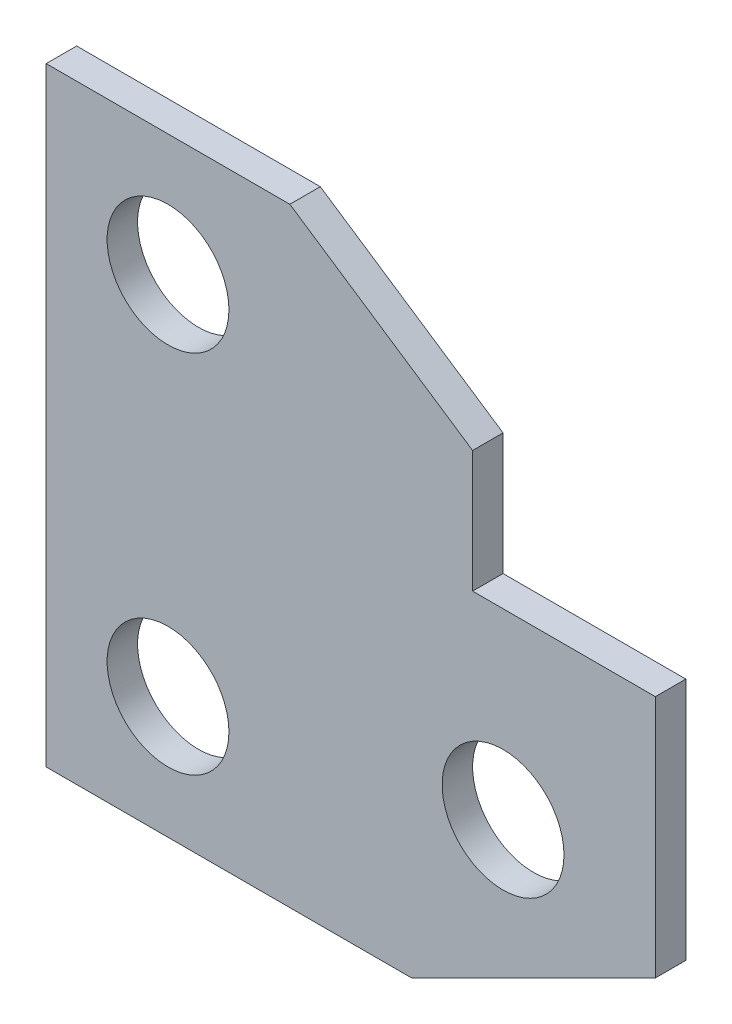
SolidWorks part; units mm, degrees
ref_plane "Front Plane" through (0, 0, 0) normal (0, 0, 1) x (1, 0, 0)
ref_plane "Top Plane" through (0, 0, 0) normal (0, 1, 0) x (1, 0, 0)
ref_plane "Right Plane" through (0, 0, 0) normal (1, 0, 0) x (0, 0, -1)
sketch "Sketch1" plane through (0, 0, 0) normal (0, 0, 1) x (1, 0, 0)
  line L0 (-73.2941, 93.7647) -> (-73.2941, -6.2353)
  line L1 (-73.2941, -6.2353) -> (-13.2941, -6.2353)
  line L2 (-13.2941, -6.2353) -> (26.7059, 13.7647)
  line L3 (26.7059, 13.7647) -> (26.7059, 53.7647)
  line L4 (26.7059, 53.7647) -> (-3.2941, 53.7647)
  line L5 (-3.2941, 73.7647) -> (-33.2941, 93.7647)
  line L6 (-33.2941, 93.7647) -> (-73.2941, 93.7647)
  line L7 (-3.2941, 73.7647) -> (-3.2941, 53.7647)
  circle A0 centre (-53.2941, 73.7647) radius 10
  circle A1 centre (-53.2941, 13.7647) radius 10
  circle A2 centre (1.7059, 23.7647) radius 10
  point P13 (0, 0)
  point P15 (6.987, 24.1007)
  point P16 (0, 0)
  point P17 (0, 0)
  dimension "D2" = 20
  dimension "D3" = 20
  dimension "D4" = 20
  dimension "D9" = 100
  dimension "D1" = 60
  dimension "D5" = 100
  dimension "D6" = 40
  dimension "D7" = 20
  dimension "D8" = 60
  dimension "D10" = 75
  dimension "D11" = 60
  dimension "D12" = 20
  dimension "D13" = 30
  dimension "D14" = 70
other "AlignGroup1"
other "AlignGroup2"
other "AlignGroup3"
other "AlignGroup4"
extrude "Boss-Extrude1" add sketch "Sketch1" along normal blind 5
